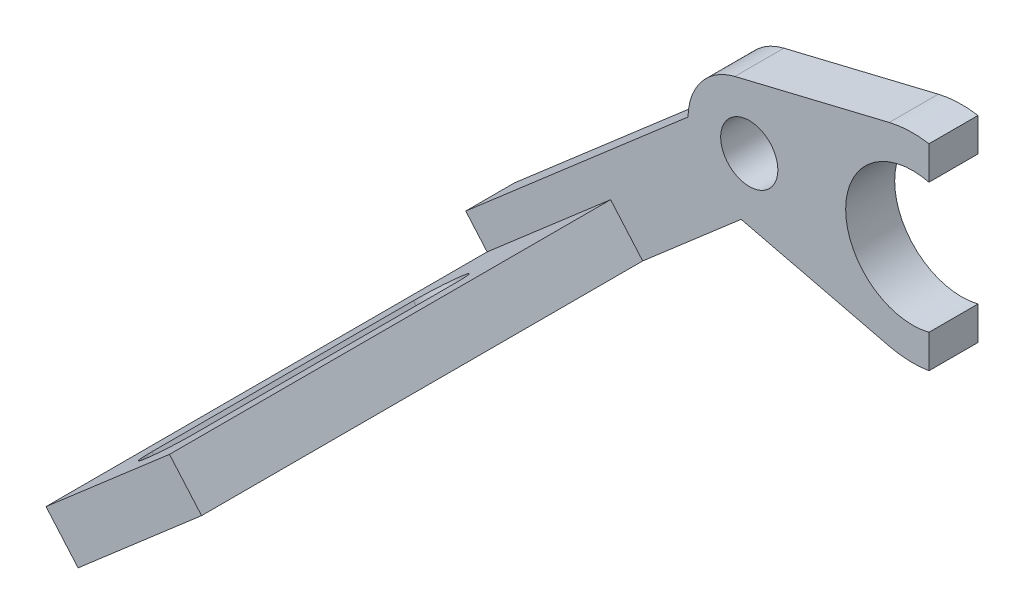
SolidWorks part; units mm, degrees
ref_plane "Plano frontal" through (0, 0, 0) normal (0, 0, 1) x (1, 0, 0)
ref_plane "Plano superior" through (0, 0, 0) normal (0, 1, 0) x (1, 0, 0)
ref_plane "Plano direito" through (0, 0, 0) normal (1, 0, 0) x (0, 0, -1)
sketch "Esboço1" plane through (0, 0, 0) normal (0, 0, 1) x (1, 0, 0)
  line L0 (-0.8812, 3.645) -> (8.5665, 5.9292)
  line L1 (-0.8812, -3.645) -> (8.5665, -5.9292)
  line L2 (11, 6.0175) -> (11, 3.9762)
  line L3 (11, -3.9762) -> (11, -6.0175)
  line L4 (-3.7495, 0.0596) -> (-17.3549, -11.7258)
  line L5 (-3.7495, 0.0596) -> (-0.4758, -3.7197) construction
  line L6 (-0.4758, -3.7197) -> (-14.0812, -15.505)
  line L7 (-14.0812, -15.505) -> (-17.3549, -11.7258)
  line L8 (0, 0) -> (-15.718, -13.6154) construction
  line L9 (0, 0) -> (12.4543, 0) construction
  circle A0 centre (0, 0) radius 1.75
  arc A1 (8.5665, -5.9292) -> (11, -6.0175) centre (10, 0) ccw
  arc A2 (11, 3.9762) -> (11, -3.9762) centre (10, 0) ccw
  arc A3 (-0.8812, 3.645) -> (-3.7495, 0.0596) centre (0, 0) ccw
  arc A4 (11, 6.0175) -> (8.5665, 5.9292) centre (10, 0) ccw
  arc A5 (-0.4758, -3.7197) -> (-0.8812, -3.645) centre (0, 0) ccw
  point P15 (-2.1127, -1.8301)
  point P17 (-15.718, -13.6154)
  dimension "D1" = 8.2
  dimension "D3" = 2
  dimension "D4" = 3.5
  dimension "D5" = 2
  dimension "D2" = 10
  dimension "D6" = 18
  dimension "D7" = 5
  dimension "D8" = 40.9
  dimension "D9" = 1
extrude "Ressalto-extrusão1" add sketch "Esboço1" along normal blind 3 contours A3 A5 L1 L6 A0 | A5 L6 L1 A1 L3 A2 L2 A4 L0 | A5 L4 L7 L6 L1
sketch "Esboço2" plane through (1.6369, -1.8896, 0) normal (0.6547, -0.7559, 0) x (0.7559, 0.6547, 0)
  line L0 (-14.0951, 26) -> (-14.0951, 10)
  line L1 (-20.7951, 0) -> (-10.7951, 0)
  line L2 (-20.7951, 0) -> (-20.7951, 30)
  line L3 (-20.7951, 30) -> (-10.7951, 30)
  line L4 (-10.7951, 0) -> (-10.7951, 30)
  line L5 (-17.4951, 26) -> (-17.4951, 10)
  arc A0 (-14.0951, 26) -> (-17.4951, 26) centre (-15.7951, 26) ccw
  arc A1 (-17.4951, 10) -> (-14.0951, 10) centre (-15.7951, 10) ccw
  point P10 (-15.7951, 30)
  dimension "D4" = 3.4
  dimension "D1" = 30
  dimension "D2" = 10
  dimension "D3" = 16
  dimension "D5" = 4
extrude "Ressalto-extrusão2" add sketch "Esboço2" against normal blind 3
